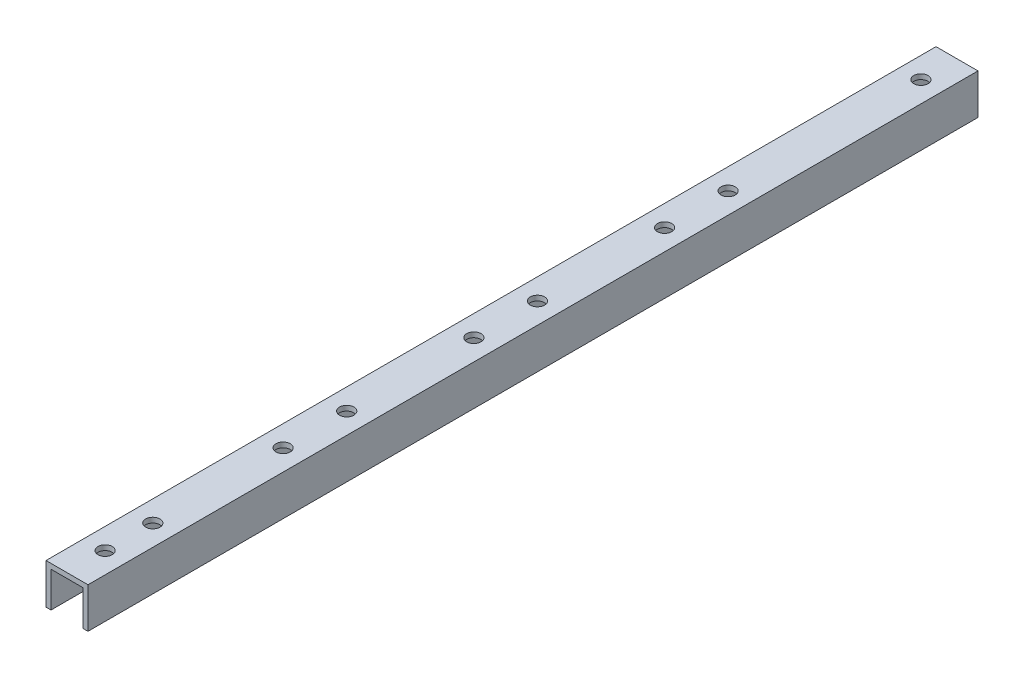
SolidWorks part; units mm, degrees
ref_plane "Front Plane" through (0, 0, 0) normal (0, 0, 1) x (1, 0, 0)
ref_plane "Top Plane" through (0, 0, 0) normal (0, 1, 0) x (1, 0, 0)
ref_plane "Right Plane" through (0, 0, 0) normal (1, 0, 0) x (0, 0, -1)
sketch "Sketch1" plane through (0, 0, 0) normal (0, 0, 1) x (1, 0, 0)
  line L0 (0, 0) -> (0, -1.5875) construction
  line L1 (-6.604, 0) -> (6.604, 0)
  line L2 (6.604, 0) -> (6.604, -12.7)
  line L3 (6.604, -12.7) -> (5.0165, -12.7)
  line L4 (5.0165, -12.7) -> (5.0165, -1.5875)
  line L5 (5.0165, -1.5875) -> (-5.0165, -1.5875)
  line L6 (-5.0165, -12.7) -> (-5.0165, -1.5875)
  line L7 (-6.604, -12.7) -> (-5.0165, -12.7)
  line L8 (-6.604, 0) -> (-6.604, -12.7)
  point P5 (0, -1.6377)
  dimension "D1" = 12.7
  dimension "D2" = 1.5875
  dimension "D3" = 13.208
extrude "Boss-Extrude1" add sketch "Sketch1" against normal blind 260 and the other way blind 20
hole_wizard "M4 Clearance Hole1" positions "Sketch2" profile "Sketch3" hole size "M4" standard "ANSI Metric" end condition through all
sketch "Sketch2" plane through (0, 0, 0) normal (0, 1, 0) x (1, 0, 0)
  line L0 (6.604, -20) -> (-6.604, -20) construction
  point P0 (0, 7)
  point P2 (0, 248.64)
  point P7 (0, 0)
  point P9 (0, 0)
  dimension "D1" = 241.64
  dimension "D2" = 27
sketch "Sketch3" plane through (0, 0, -7) normal (1, 0, 0) x (0, 0, 1)
  line L0 (0, 0) -> (0, 12.7)
  line L1 (0, 12.7) -> (2.25, 12.7)
  line L2 (2.25, 12.7) -> (2.25, 0)
  line L5 (2.25, 0) -> (0, 0)
  line L11 (0, -6.35) -> (0, 107.95) construction
  dimension "Thru Hole Dia." = 4.5
  dimension "Thru Hole Depth" = 12.7
hole_wizard "M4 Clearance Hole2" positions "Sketch4" profile "Sketch5" hole size "M4" standard "ANSI Metric" end condition through all
sketch "Sketch4" plane through (0, 0, 0) normal (0, 1, 0) x (1, 0, 0)
  circle A0 centre (0, 7) radius 2.25 construction
  point P0 (0, 108)
  point P2 (0, 128)
  point P9 (0, -8)
  point P12 (0, 188)
  point P14 (0, 168)
  point P16 (0, 68)
  point P18 (0, 48)
  point P21 (0, 0)
  point P22 (0, 0)
  dimension "D3" = 15
  dimension "D1" = 101
  dimension "D2" = 20
  dimension "D4" = 20
  dimension "D5" = 20
  dimension "D6" = 60
  dimension "D7" = 60
sketch "Sketch5" plane through (0, 0, -108) normal (1, 0, 0) x (0, 0, 1)
  line L0 (0, 0) -> (0, 12.7)
  line L1 (0, 12.7) -> (2.25, 12.7)
  line L2 (2.25, 12.7) -> (2.25, 0)
  line L5 (2.25, 0) -> (0, 0)
  line L11 (0, -6.35) -> (0, 107.95) construction
  dimension "Thru Hole Dia." = 4.5
  dimension "Thru Hole Depth" = 12.7
